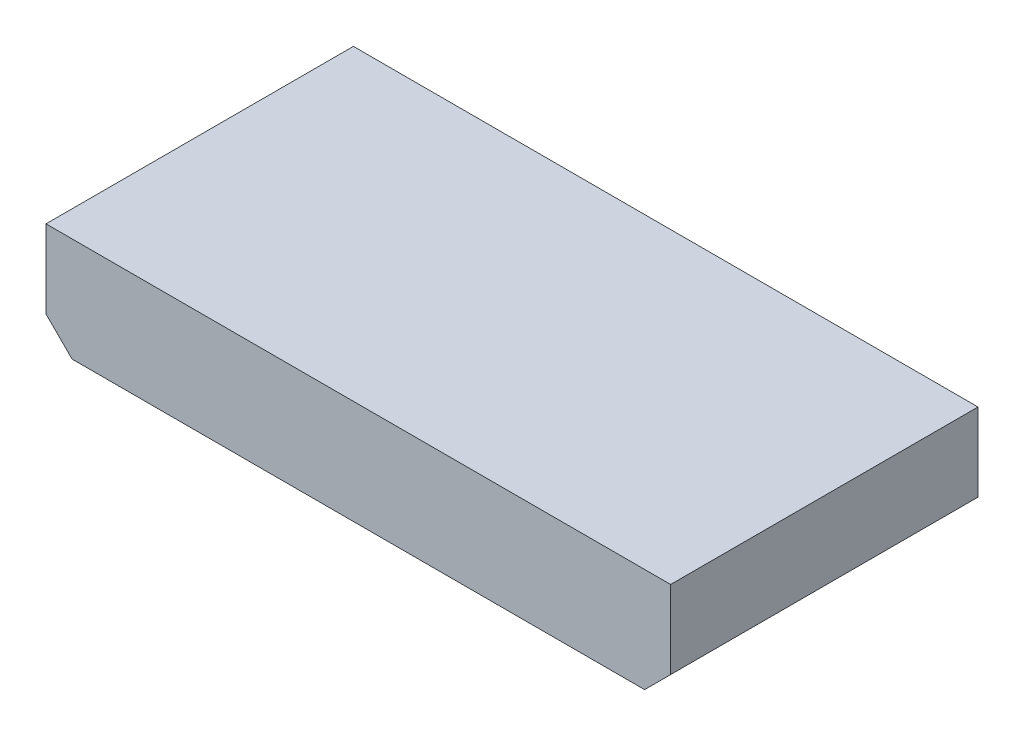
SolidWorks part; units mm, degrees
ref_plane "Front Plane" through (0, 0, 0) normal (0, 0, 1) x (1, 0, 0)
ref_plane "Top Plane" through (0, 0, 0) normal (0, 1, 0) x (1, 0, 0)
ref_plane "Right Plane" through (0, 0, 0) normal (1, 0, 0) x (0, 0, -1)
sketch "Sketch1" plane through (0, 0, 0) normal (0, 0, 1) x (1, 0, 0)
  line L0 (-5.08, 2.54) -> (-5.08, -1.27)
  line L1 (-5.08, -1.27) -> (-3.81, -2.54)
  line L2 (-3.81, -2.54) -> (24.13, -2.54)
  line L3 (24.13, -2.54) -> (25.4, -1.27)
  line L4 (25.4, -1.27) -> (25.4, 2.54)
  line L5 (25.4, 2.54) -> (-5.08, 2.54)
extrude "Component_Outline" add sketch "Sketch1" along normal blind 15 separate body
sketch "Sketch2" plane through (0, 0, 0) normal (0, 0, 1) x (1, 0, 0)
  circle A0 centre (0, 0) radius 0.25
extrude "1" add sketch "Sketch2" against normal blind 2 separate body
sketch "Sketch3" plane through (0, 0, 0) normal (0, 0, 1) x (1, 0, 0)
  circle A0 centre (2.54, 0) radius 0.25
extrude "2" add sketch "Sketch3" against normal blind 2 separate body
sketch "Sketch4" plane through (0, 0, 0) normal (0, 0, 1) x (1, 0, 0)
  circle A0 centre (5.08, 0) radius 0.25
extrude "3" add sketch "Sketch4" against normal blind 2 separate body
sketch "Sketch5" plane through (0, 0, 0) normal (0, 0, 1) x (1, 0, 0)
  circle A0 centre (7.62, 0) radius 0.25
extrude "4" add sketch "Sketch5" against normal blind 2 separate body
sketch "Sketch6" plane through (0, 0, 0) normal (0, 0, 1) x (1, 0, 0)
  circle A0 centre (10.16, 0) radius 0.25
extrude "5" add sketch "Sketch6" against normal blind 2 separate body
sketch "Sketch7" plane through (0, 0, 0) normal (0, 0, 1) x (1, 0, 0)
  circle A0 centre (12.7, 0) radius 0.25
extrude "6" add sketch "Sketch7" against normal blind 2 separate body
sketch "Sketch8" plane through (0, 0, 0) normal (0, 0, 1) x (1, 0, 0)
  circle A0 centre (15.24, 0) radius 0.25
extrude "7" add sketch "Sketch8" against normal blind 2 separate body
sketch "Sketch9" plane through (0, 0, 0) normal (0, 0, 1) x (1, 0, 0)
  circle A0 centre (17.78, 0) radius 0.25
extrude "8" add sketch "Sketch9" against normal blind 2 separate body
sketch "Sketch10" plane through (0, 0, 0) normal (0, 0, 1) x (1, 0, 0)
  circle A0 centre (20.32, 0) radius 0.25
extrude "9" add sketch "Sketch10" against normal blind 2 separate body
sketch3d "3DSketch1"
  line L0 (0, 0, 0) -> (1, 0, 0)
  line L1 (0, 0, 0) -> (0, 1, 0)
  line L2 (0, 0, 0) -> (0, 0, 1)
  point P0 (0, 0, 0)
